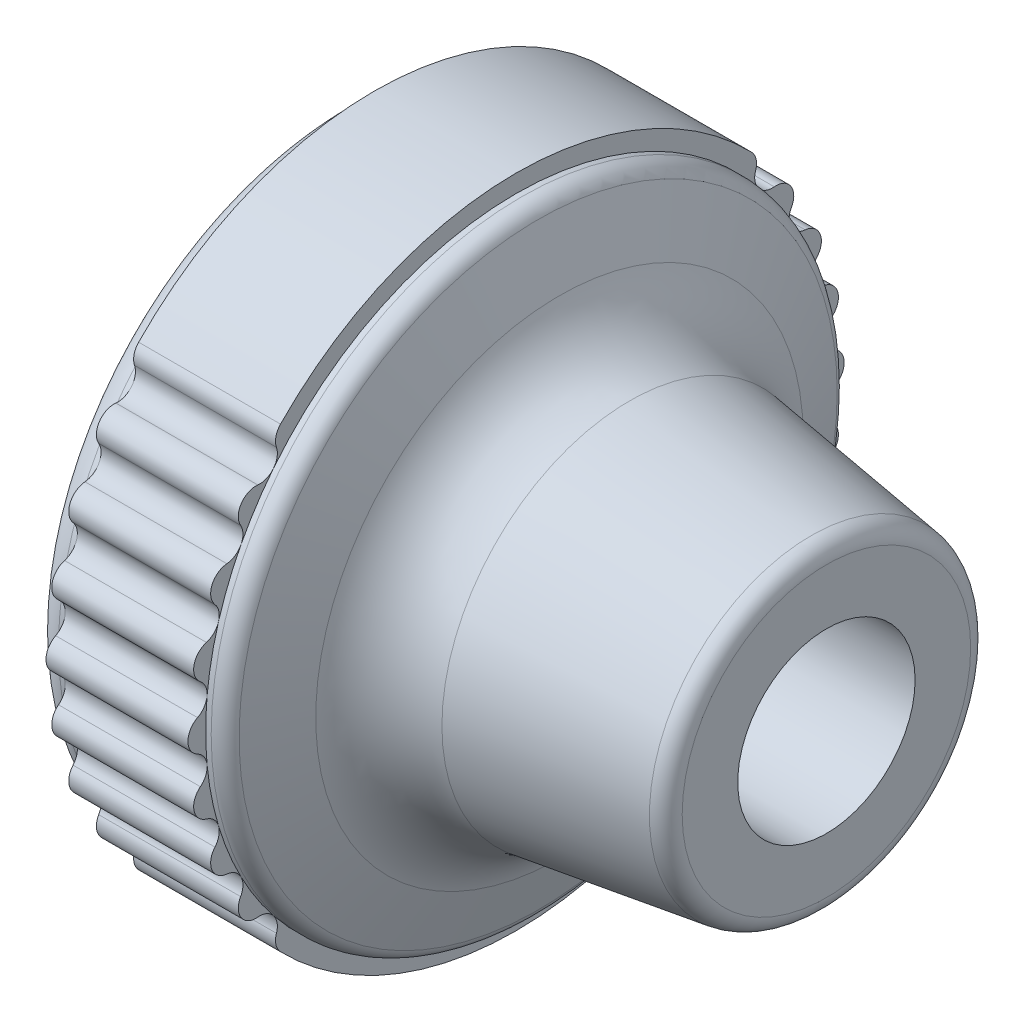
SolidWorks part; units mm, degrees
ref_plane "face" through (0, 0, 0) normal (0, 0, 1) x (1, 0, 0)
ref_plane "dessus" through (0, 0, 0) normal (0, 1, 0) x (1, 0, 0)
ref_plane "coté" through (0, 0, 0) normal (1, 0, 0) x (0, 0, -1)
sketch "Esquisse1" plane through (0, 0, 0) normal (0, 0, 1) x (1, 0, 0)
  line L0 (95.2605, 0) -> (-92.7584, 0) construction
  line L1 (0, 17.5) -> (0, 18.5)
  line L2 (0, 18.5) -> (8, 18.5)
  line L3 (8, 18.5) -> (8, 17.5)
  line L4 (8, 17.5) -> (8.3132, 17.5)
  line L5 (9.2465, 16.859) -> (10.4463, 13.7397)
  line L6 (14.4059, 10.5849) -> (24.6414, 9.1227)
  line L7 (25.5, 8.1327) -> (25.5, 0)
  line L8 (0, 17.5) -> (-0.2924, 17.5)
  line L9 (25.5, 0) -> (-4.5, 0)
  arc A0 (9.2465, 16.859) -> (8.3132, 17.5) centre (8.3132, 16.5) ccw
  arc A1 (24.6414, 9.1227) -> (25.5, 8.1327) centre (24.5, 8.1327) cw
  arc A2 (14.4059, 10.5849) -> (10.4463, 13.7397) centre (15.113, 15.5346) cw
  arc A3 (-1.7087, 16.4942) -> (-4.5, 0) centre (45.5, 0.0217) ccw
  arc A4 (-1.7087, 16.4942) -> (-0.2924, 17.5) centre (-0.2924, 16) cw
  point P14 (9, 17.5)
  point P17 (25.5, 9)
  point P20 (11.5, 11)
  dimension "D9" = 1
  dimension "D10" = 1
  dimension "D11" = 5
  dimension "D13" = 30
  dimension "D14" = 1.5
  dimension "D12" = 50
  dimension "D1" = 18.5
  dimension "D2" = 8
  dimension "D3" = 17.5
  dimension "D4" = 17.5
  dimension "D5" = 14
  dimension "D6" = 1
  dimension "D7" = 11
  dimension "D8" = 9
revolve "Base-Révolution" add sketch "Esquisse1" angle 360 about L0
hole_wizard "Perçage1" positions "Esquisse3" profile "Esquisse2" legacy
sketch "Esquisse3" plane through (25.5, 0, 0) normal (1, 0, 0) x (0, 0, -1)
  point P0 (0, 0)
sketch "Esquisse2" plane through (25.5, 0, 0) normal (0, 1, 0) x (0, 0, -1)
  line L0 (0, 0) -> (0, 23.5043)
  line L1 (0, 23.5043) -> (5, 20.5)
  line L2 (5, 20.5) -> (5, 0)
  line L4 (5, 0) -> (0, 0)
  line L6 (0, 23.5043) -> (-5, 20.5) construction
  line L7 (0, -4.2442) -> (0, 117.3081) construction
  dimension "Diamètre" = 10
  dimension "Profondeur" = 20.5
  dimension "Angle" = 118
sketch "Esquisse4" plane through (8, 0, 0) normal (1, 0, 0) x (0, 0, -1)
  line L0 (0, 19.5346) -> (0, -20.6236) construction
  line L1 (19.7047, 0) -> (-23.4483, 0) construction
  line L2 (0, 0) -> (-18.6089, 18.053) construction
  line L3 (0, 0) -> (-12.5606, -12.1853) construction
  line L4 (0, 0) -> (-17.5, 0) construction
  arc A0 (-17.9571, 0.8894) -> (-17.9571, -0.8894) centre (-17.5, 0) ccw
  circle A1 centre (0, 0) radius 18.5 construction
  arc A2 (13.2783, -12.8816) -> (13.508, -11.8653) centre (12.5606, -12.1853) ccw
  arc A3 (-17.9571, 0.8894) -> (-17.7954, 2.5642) centre (-18.4143, 1.7788) ccw
  circle A4 centre (0, 0) radius 17.5 construction
  arc A5 (-17.4549, 4.3101) -> (-17.7954, 2.5642) centre (-17.1764, 3.3497) ccw
  arc A6 (-17.4549, 4.3101) -> (-16.9746, 5.922) centre (-17.7333, 5.2706) ccw
  arc A7 (14.559, -10.5506) -> (13.508, -11.8653) centre (14.4554, -11.5452) ccw
  arc A8 (-16.3023, 7.5768) -> (-16.9746, 5.922) centre (-16.2125, 6.5763) ccw
  arc A9 (-16.3023, 7.5768) -> (-15.5272, 9.0638) centre (-16.3913, 8.5687) ccw
  arc A10 (-14.559, 10.5506) -> (-15.5272, 9.0638) centre (-14.6624, 9.5593) ccw
  arc A11 (-14.559, 10.5506) -> (-13.508, 11.8653) centre (-14.4554, 11.5452) ccw
  arc A12 (-13.2783, 12.8816) -> (-13.508, 11.8653) centre (-12.5606, 12.1853) ccw
  arc A13 (-17.9571, -0.8894) -> (-17.7954, -2.5642) centre (-18.4143, -1.7788) cw
  arc A14 (-17.4549, -4.3101) -> (-17.7954, -2.5642) centre (-17.1764, -3.3497) cw
  arc A15 (-17.4549, -4.3101) -> (-16.9746, -5.922) centre (-17.7333, -5.2706) cw
  arc A16 (-16.3023, -7.5768) -> (-16.9746, -5.922) centre (-16.2125, -6.5763) cw
  arc A17 (-16.3023, -7.5768) -> (-15.5272, -9.0638) centre (-16.3913, -8.5687) cw
  arc A18 (-14.559, -10.5506) -> (-15.5272, -9.0638) centre (-14.6624, -9.5593) cw
  arc A19 (-14.559, -10.5506) -> (-13.508, -11.8653) centre (-14.4554, -11.5452) cw
  arc A20 (-13.2783, -12.8816) -> (-13.508, -11.8653) centre (-12.5606, -12.1853) cw
  arc A21 (14.559, -10.5506) -> (15.5272, -9.0638) centre (14.6624, -9.5593) ccw
  arc A22 (16.3023, -7.5768) -> (15.5272, -9.0638) centre (16.3913, -8.5687) ccw
  arc A23 (16.3023, -7.5768) -> (16.9746, -5.922) centre (16.2125, -6.5763) ccw
  arc A24 (17.4549, -4.3101) -> (16.9746, -5.922) centre (17.7333, -5.2706) ccw
  arc A25 (17.4549, -4.3101) -> (17.7954, -2.5642) centre (17.1764, -3.3497) ccw
  arc A26 (17.9571, -0.8894) -> (17.7954, -2.5642) centre (18.4143, -1.7788) ccw
  arc A27 (13.2783, 12.8816) -> (13.508, 11.8653) centre (12.5606, 12.1853) cw
  arc A28 (14.559, 10.5506) -> (13.508, 11.8653) centre (14.4554, 11.5452) cw
  arc A29 (14.559, 10.5506) -> (15.5272, 9.0638) centre (14.6624, 9.5593) cw
  arc A30 (16.3023, 7.5768) -> (15.5272, 9.0638) centre (16.3913, 8.5687) cw
  arc A31 (16.3023, 7.5768) -> (16.9746, 5.922) centre (16.2125, 6.5763) cw
  arc A32 (17.4549, 4.3101) -> (16.9746, 5.922) centre (17.7333, 5.2706) cw
  arc A33 (17.4549, 4.3101) -> (17.7954, 2.5642) centre (17.1764, 3.3497) cw
  arc A34 (17.9571, 0.8894) -> (17.7954, 2.5642) centre (18.4143, 1.7788) cw
  arc A35 (17.9571, 0.8894) -> (17.9571, -0.8894) centre (17.5, 0) cw
  arc A37 (13.2783, 12.8816) -> (-13.2783, 12.8816) centre (0, 0) ccw
  circle A38 centre (0, 0) radius 18.5
  arc A39 (-13.2783, -12.8816) -> (13.2783, -12.8816) centre (0, 0) ccw
  dimension "D1" = 0
extrude "Enlèv. mat.-Extru.2" cut sketch "Esquisse4" against normal through all flip side to cut
